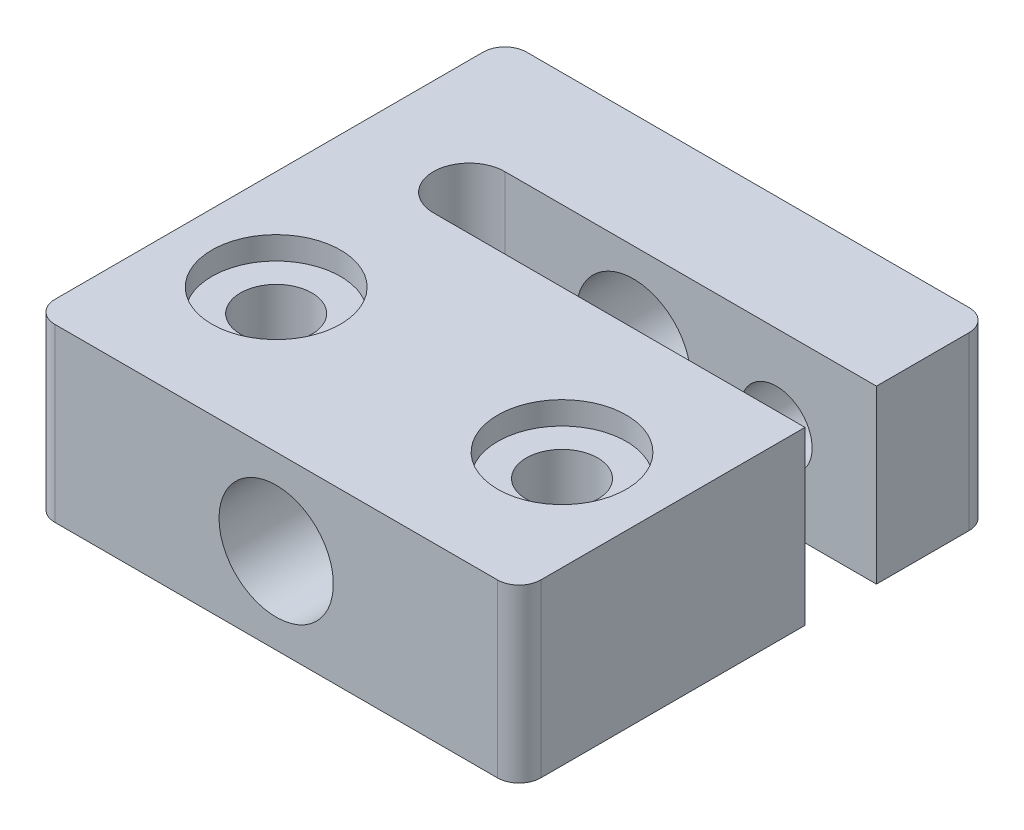
SolidWorks part; units mm, degrees
ref_plane "Front" through (0, 0, 0) normal (0, 0, 1) x (1, 0, 0)
ref_plane "Top" through (0, 0, 0) normal (0, 1, 0) x (1, 0, 0)
ref_plane "Right" through (0, 0, 0) normal (1, 0, 0) x (0, 0, -1)
sketch "Sketch1" plane through (0, 0, 0) normal (0, 1, 0) x (1, 0, 0)
  line L0 (-15.48, 0) -> (15.48, 0)
  line L1 (-17, 1.52) -> (-17, 31.48)
  line L2 (17, 1.52) -> (17, 20)
  line L3 (-15.48, 33) -> (15.48, 33)
  line L4 (17, 31.48) -> (17, 25)
  line L5 (17, 25) -> (-9, 25)
  line L6 (-9, 25) -> (-9, 20) construction
  line L7 (-9, 20) -> (17, 20)
  line L8 (17, 20) -> (17, 22.5) construction
  line L9 (-9, 22.5) -> (17, 22.5) construction
  line L10 (-17, 10) -> (17, 10) construction
  line L11 (0, 33) -> (0, 0) construction
  arc A0 (-17, 1.52) -> (-15.48, 0) centre (-15.48, 1.52) ccw
  arc A1 (15.48, 0) -> (17, 1.52) centre (15.48, 1.52) ccw
  arc A2 (-15.48, 33) -> (-17, 31.48) centre (-15.48, 31.48) ccw
  arc A3 (17, 31.48) -> (15.48, 33) centre (15.48, 31.48) ccw
  arc A4 (-9, 25) -> (-9, 20) centre (-9, 22.5) ccw
  circle A5 centre (-10, 10) radius 2.5
  circle A6 centre (10, 10) radius 2.5
  point P27 (0, 10)
  dimension "D1" = 5
  dimension "D2" = 3.04
  dimension "D4" = 26
  dimension "D7" = 20
  dimension "D6" = 34
  dimension "D9" = 5
  dimension "D3" = 33
  dimension "D5" = 8
  dimension "D8" = 10
extrude "Boss-Extrude1" add sketch "Sketch1" along normal blind 12
sketch "Sketch2" plane through (0, 12, 0) normal (0, 1, 0) x (1, 0, 0)
  circle A0 centre (-10, 10) radius 4.5
  circle A1 centre (10, 10) radius 4.5
  dimension "D1" = 9
extrude "Cut-Extrude1" cut sketch "Sketch2" against normal blind 1.6
sketch "Sketch3" plane through (0, 0, 0) normal (0, -1, 0) x (1, 0, 0)
  line L0 (-17, -31.48) -> (-17, -1.52) construction
  line L1 (6, -7.6906) -> (6, -12.3094)
  line L2 (6, -12.3094) -> (10, -14.6188)
  line L3 (10, -14.6188) -> (14, -12.3094)
  line L4 (14, -12.3094) -> (14, -7.6906)
  line L5 (14, -7.6906) -> (10, -5.3812)
  line L6 (10, -5.3812) -> (6, -7.6906)
  line L7 (-14, -12.3094) -> (-10, -14.6188)
  line L8 (-10, -14.6188) -> (-6, -12.3094)
  line L9 (-6, -12.3094) -> (-6, -7.6906)
  line L10 (-6, -7.6906) -> (-10, -5.3812)
  line L11 (-10, -5.3812) -> (-14, -7.6906)
  line L12 (-14, -7.6906) -> (-14, -12.3094)
  circle A0 centre (10, -10) radius 4 construction
  circle A1 centre (-10, -10) radius 4 construction
  dimension "D1" = 8
extrude "Cut-Extrude2" cut sketch "Sketch3" against normal blind 4.97
sketch "Sketch4" plane through (0, 0, -33) normal (0, 0, -1) x (-1, 0, 0)
  line L0 (15.48, 6) -> (-15.48, 6) construction
  line L1 (15.48, 12) -> (15.48, 0) construction
  line L2 (-15.48, 12) -> (-15.48, 0) construction
  line L3 (0, 0) -> (0, 12) construction
  line L4 (-15.48, 12) -> (15.48, 12) construction
  circle A0 centre (0, 6) radius 4
  point P11 (0, 6)
  dimension "D1" = 8
extrude "Cut-Extrude3" cut sketch "Sketch4" against normal through all
sketch "Sketch5" plane through (0, 0, -33) normal (0, 0, -1) x (-1, 0, 0)
  line L0 (15.48, 6) -> (-15.48, 6) construction
  line L1 (15.48, 12) -> (15.48, 0) construction
  line L2 (-15.48, 12) -> (-15.48, 0) construction
  line L3 (0, 0) -> (0, 12) construction
  line L4 (-15.48, 0) -> (15.48, 0) construction
  line L5 (-15.48, 12) -> (15.48, 12) construction
  circle A0 centre (-10, 6) radius 2.5
  point P14 (0, 6)
  dimension "D2" = 5
  dimension "D1" = 10
extrude "Cut-Extrude4" cut sketch "Sketch5" against normal up to next
